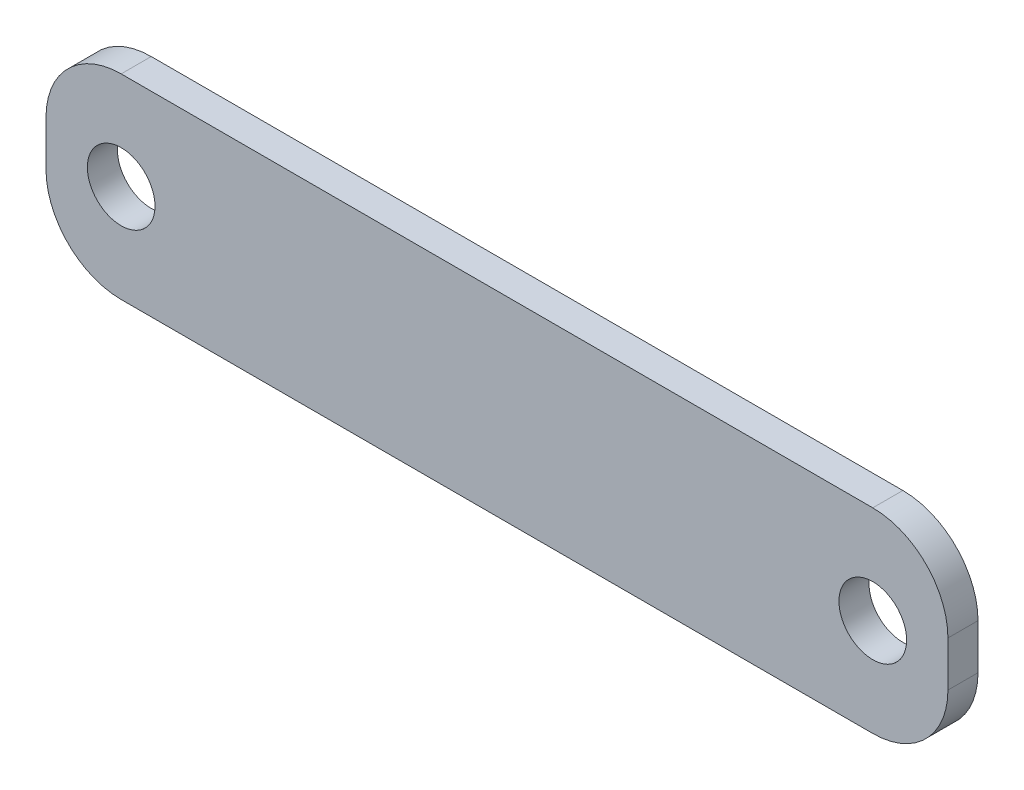
SolidWorks part; units mm, degrees
ref_plane "Plan de face" through (0, 0, 0) normal (0, 0, 1) x (1, 0, 0)
ref_plane "Plan de dessus" through (0, 0, 0) normal (0, 1, 0) x (1, 0, 0)
ref_plane "Plan de droite" through (0, 0, 0) normal (1, 0, 0) x (0, 0, -1)
sketch "Esquisse1" plane through (0, 0, 0) normal (0, 0, 1) x (1, 0, 0)
  line L0 (-1005, 0) -> (48995, 0) construction
  line L1 (0, 6.5) -> (50, 6.5)
  line L2 (-5, 1.5) -> (-5, -1.5)
  line L3 (0, -6.5) -> (50, -6.5)
  line L4 (55, 1.5) -> (55, -1.5)
  circle A0 centre (0, 0) radius 2.25
  circle A1 centre (50, 0) radius 2.25
  arc A2 (50, 6.5) -> (55, 1.5) centre (50, 1.5) cw
  arc A3 (50, -6.5) -> (55, -1.5) centre (50, -1.5) ccw
  arc A4 (-5, -1.5) -> (0, -6.5) centre (0, -1.5) ccw
  arc A5 (0, 6.5) -> (-5, 1.5) centre (0, 1.5) ccw
  point P12 (-5, 0)
  point P14 (55, 6.5)
  point P17 (55, -6.5)
  point P22 (-5, 6.5)
  dimension "D1" = 4.5
  dimension "D3" = 4.5
  dimension "D7" = 5
  dimension "D2" = 60
  dimension "D4" = 5
  dimension "D5" = 5
  dimension "D6" = 13
extrude "Boss.-Extru.1" add sketch "Esquisse1" along normal blind 2
